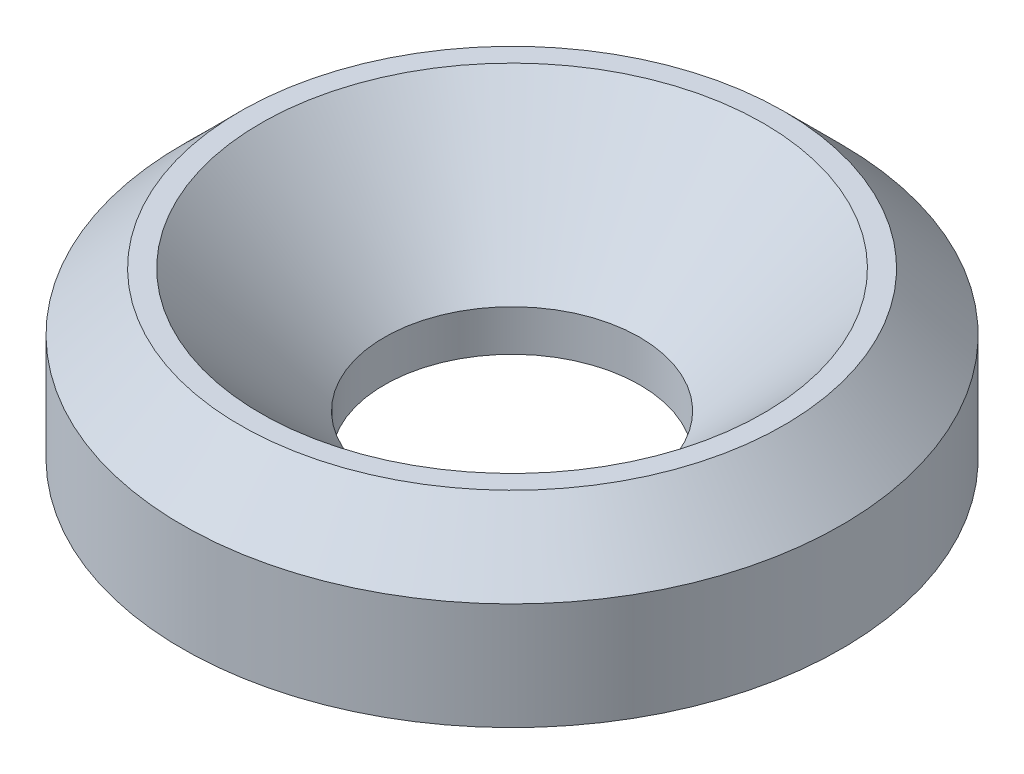
SolidWorks part; units mm, degrees
material "6061 Alloy"
ref_plane "Front" through (0, 0, 0) normal (0, 0, 1) x (1, 0, 0)
ref_plane "Top" through (0, 0, 0) normal (0, 1, 0) x (1, 0, 0)
ref_plane "Right" through (0, 0, 0) normal (1, 0, 0) x (0, 0, -1)
sketch "Sketch1" plane through (0, 0, 0) normal (0, 0, 1) x (1, 0, 0)
  line L0 (0, 0) -> (0, 2) construction
  line L1 (4, 0) -> (4, 1.3)
  line L2 (4, 1.3) -> (3.3, 2)
  line L3 (3.3, 2) -> (3.05, 2)
  line L4 (3.05, 2) -> (1.55, 0.5)
  line L5 (1.55, 0.5) -> (1.55, 0)
  line L6 (1.55, 0) -> (4, 0)
  line L7 (0, 4.6069) -> (0, 2) construction
  line L8 (0, 4.6069) -> (0, 8.6069) construction
  circle A0 centre (0, 4.6069) radius 4 construction
  point P11 (0, 0)
  dimension "D9" = 8
  dimension "D1" = 8
  dimension "D2" = 2
  dimension "D3" = 3.1
  dimension "D4" = 6.6
  dimension "D5" = 6.1
  dimension "D6" = 45
  dimension "D7" = 0.7
  dimension "D10" = 8.6069
revolve "Revolve1" add sketch "Sketch1" angle 360 about L0
